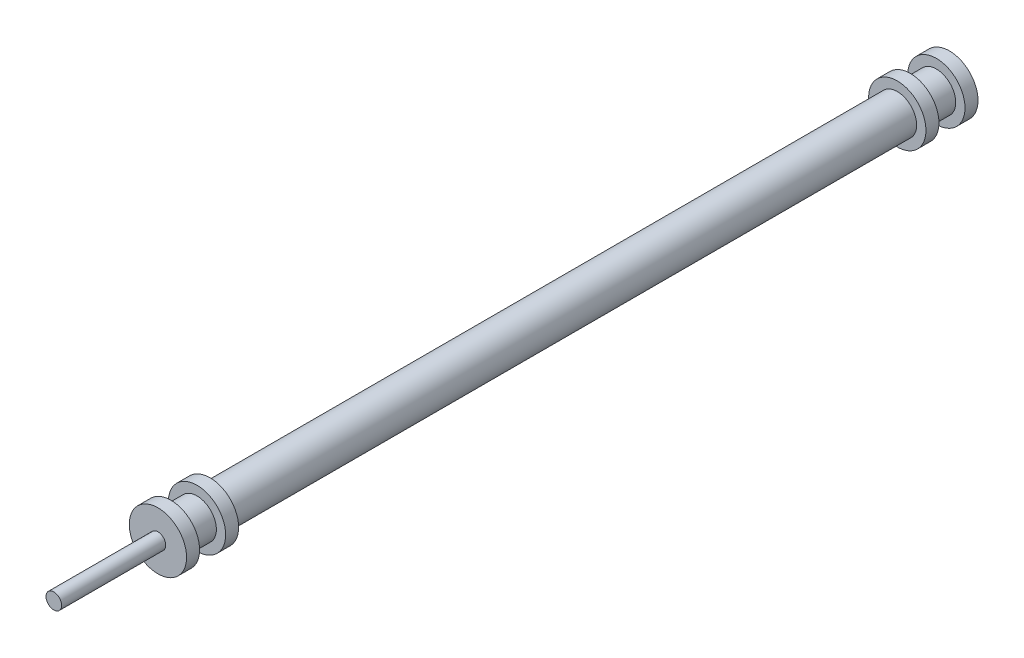
SolidWorks part; units mm, degrees
ref_plane "Front Plane" through (0, 0, 0) normal (0, 0, 1) x (1, 0, 0)
ref_plane "Top Plane" through (0, 0, 0) normal (0, 1, 0) x (1, 0, 0)
ref_plane "Right Plane" through (0, 0, 0) normal (1, 0, 0) x (0, 0, -1)
sketch "Sketch1" plane through (0, 0, 0) normal (0, 0, 1) x (1, 0, 0)
  circle A0 centre (0, 0) radius 3.725
  dimension "D1" = 7.45
extrude "Boss-Extrude1" add sketch "Sketch1" along normal blind 132
ref_plane "Plane1" through (0, 0, 66) normal (0, 0, 1) x (1, 0, 0)
sketch "Sketch3" plane through (0, 0, 132) normal (0, 0, 1) x (1, 0, 0)
  circle A0 centre (0, 0) radius 5.5
  dimension "D1" = 11
extrude "Boss-Extrude3" add sketch "Sketch3" along normal blind 2.5
sketch "Sketch4" plane through (0, 0, 134.5) normal (0, 0, 1) x (1, 0, 0)
  circle A0 centre (0, 0) radius 3.725
  dimension "D1" = 7.45
extrude "Boss-Extrude4" add sketch "Sketch4" along normal blind 5
sketch "Sketch5" plane through (0, 0, 139.5) normal (0, 0, 1) x (1, 0, 0)
  circle A0 centre (0, 0) radius 5.5
  dimension "D1" = 11
extrude "Boss-Extrude5" add sketch "Sketch5" along normal blind 2.5
mirror "Mirror2" about plane through (0, 0, 66) normal (0, 0, 1) of "Boss-Extrude5", "Boss-Extrude4", "Boss-Extrude3"
sketch "Sketch6" plane through (0, 0, 142) normal (0, 0, 1) x (1, 0, 0)
  circle A0 centre (0, 0) radius 1.5
  dimension "D1" = 3
extrude "Boss-Extrude6" add sketch "Sketch6" along normal blind 20
